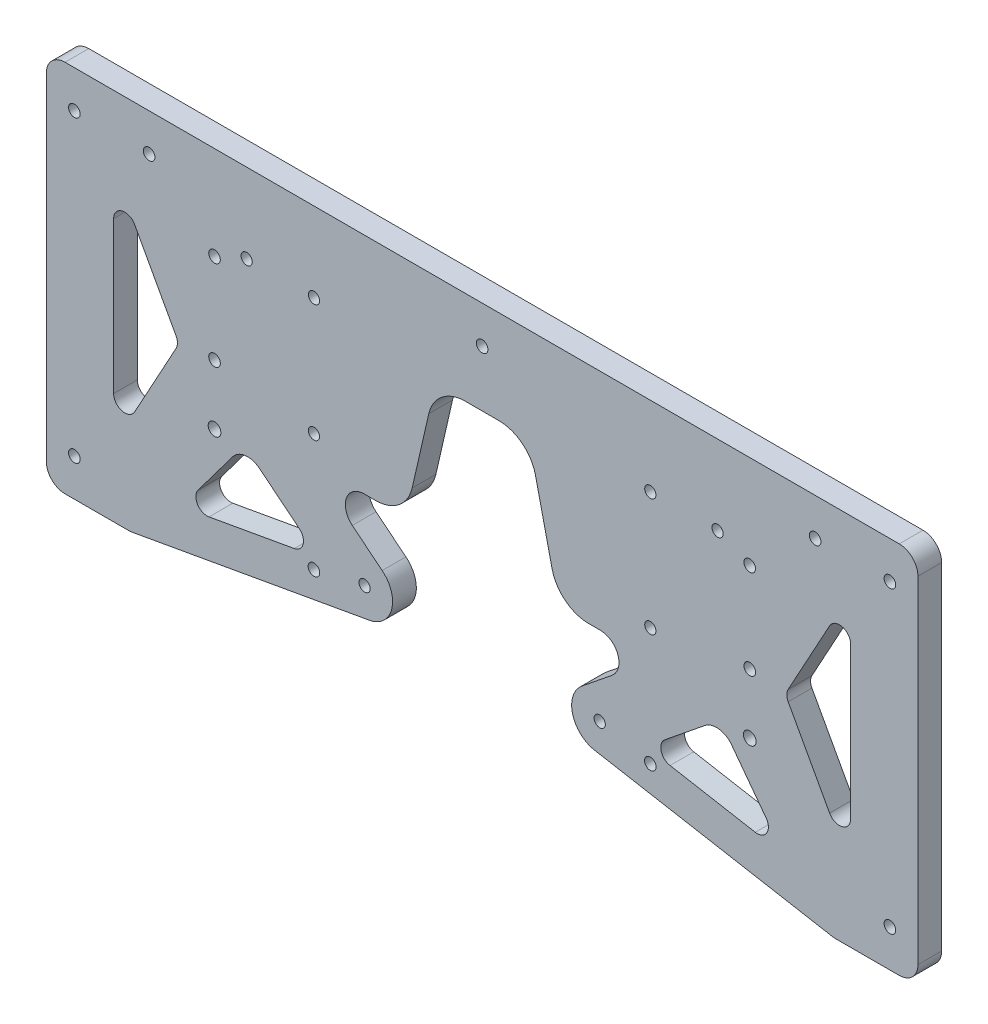
SolidWorks part; units mm, degrees
ref_plane "Front Plane" through (0, 0, 0) normal (0, 0, 1) x (1, 0, 0)
ref_plane "Top Plane" through (0, 0, 0) normal (0, 1, 0) x (1, 0, 0)
ref_plane "Right Plane" through (0, 0, 0) normal (1, 0, 0) x (0, 0, -1)
sketch "Sketch1" plane through (0, 0, 0) normal (0, 0, 1) x (1, 0, 0)
  line L0 (116.6, 0) -> (116.6, -35.2914) construction
  line L1 (0, 0) -> (233.2, 0)
  line L2 (0, 0) -> (0, -100)
  line L3 (0, -100) -> (233.2, -100)
  line L4 (233.2, 0) -> (233.2, -100)
  line L5 (0, 0) -> (15, 0)
  line L6 (0, 0) -> (0, -100)
  line L7 (0, -100) -> (15, -100)
  line L9 (233.2, 0) -> (218.2, 0)
  line L10 (233.2, 0) -> (233.2, -100)
  line L11 (233.2, -100) -> (218.2, -100)
  line L13 (0, -50) -> (37.696, -50) construction
  circle A0 centre (7.5, -10) radius 1.55
  circle A1 centre (225.7, -10) radius 1.55
  circle A2 centre (7.5, -90) radius 1.55
  circle A3 centre (225.7, -90) radius 1.55
  circle A4 centre (27.5, -10) radius 1.55
  circle A5 centre (205.7, -10) radius 1.55
  circle A6 centre (116.6, -10) radius 1.55
  dimension "D5" = 3.1
  dimension "D7" = 3.1
  dimension "D8" = 3.1
  dimension "D11" = 3.1
  dimension "D1" = 100
  dimension "D2" = 233.2
  dimension "D3" = 15
  dimension "D4" = 15
  dimension "D6" = 10
  dimension "D9" = 20
  dimension "D10" = 20
extrude "Boss-Extrude1" add sketch "Sketch1" along normal blind 6.35 contours L4 L1 L2 L3 A3 A1 A0 A2
fillet "Fillet1" radius 5 4 edges at (233.2, -100, 3.175) (0, -100, 3.175) (0, 0, 3.175) (233.2, 0, 3.175)
sketch "Sketch2" plane through (0, 0, 6.35) normal (0, 0, 1) x (1, 0, 0)
  line L0 (116.6, 0) -> (116.6, -100) construction
  line L1 (5, 0) -> (228.2, 0) construction
  line L2 (5, -100) -> (228.2, -100) construction
  line L3 (0, -5) -> (0, -95) construction
  circle A0 centre (45, -25) radius 1.55
  circle A1 centre (45, -49) radius 1.55
  circle A2 centre (188.2, -49) radius 1.55
  circle A3 centre (188.2, -25) radius 1.55
  dimension "D1" = 3.1
  dimension "D3" = 3.1
  dimension "D2" = 45
  dimension "D4" = 24
  dimension "D5" = 25
extrude "Cut-Extrude1" cut sketch "Sketch2" against normal blind 6.35 contours A0 | A1 | A2 | A3
sketch "Sketch3" plane through (0, 0, 6.35) normal (0, 0, 1) x (1, 0, 0)
  line L0 (5, 0) -> (228.2, 0) construction
  line L1 (120.7236, 0) -> (130.7236, 0)
  line L2 (120.7236, 0) -> (120.7236, 12.7)
  line L3 (120.7236, 12.7) -> (130.7236, 12.7)
  line L4 (130.7236, 0) -> (130.7236, 12.7)
  line L5 (130.7236, 24.7) -> (152.3136, 0)
  line L6 (130.7236, 12.7) -> (85.7236, 12.7)
  line L7 (130.7236, 12.7) -> (130.7236, 24.7)
  line L8 (130.7236, 24.7) -> (85.7236, 24.7)
  line L9 (85.7236, 12.7) -> (85.7236, 24.7)
  line L10 (120.7236, 12.7) -> (95.7236, 12.7)
  line L11 (120.7236, 12.7) -> (120.7236, 16.7)
  line L12 (120.7236, 16.7) -> (95.7236, 16.7)
  line L13 (95.7236, 12.7) -> (95.7236, 16.7)
  line M11 (228.2, 0) -> (5, 0)
  dimension "D1" = 12.7
  dimension "D2" = 10
  dimension "D3" = 12
  dimension "D4" = 45
  dimension "D5" = 25
  dimension "D6" = 4
extrude "Boss-Extrude2" add sketch "Sketch3" against normal up to surface (6.35 mm away) contours L4 L3 L2 M11 | L6 L13 L12 L11 L3 L7 L8 L9 | L7 L4 L5 M11 up to face at (46.55, -49, 0)
fillet "Fillet2" radius 5 1 edges at (85.7236, 12.7, 3.175)
fillet "Fillet3" radius 10 1 edges at (120.7236, 0, 3.175)
fillet "Fillet4" radius 2 1 edges at (85.7236, 24.7, 3.175)
fillet "Fillet5" radius 20 2 edges at (130.7236, 24.7, 3.175) (152.3136, 0, 3.175)
fillet "Fillet6" radius 5 1 edges at (120.7236, 16.7, 3.175)
sketch "Sketch4" plane through (0, 0, 0) normal (0, 0, -1) x (-1, 0, 0)
  line L12 (-110.7236, 0) -> (-161.3952, 0)
  line L24 (-136.7003, 17.8623) -> (-146.3368, 6.8377)
  line L25 (-87.7236, 24.7) -> (-121.642, 24.7)
  line L26 (-85.7236, 17.7) -> (-85.7236, 22.7)
  line L27 (-95.7236, 12.7) -> (-90.7236, 12.7)
  line L28 (-95.7236, 16.7) -> (-95.7236, 12.7)
  line L29 (-115.7236, 16.7) -> (-95.7236, 16.7)
  line L30 (-120.7236, 10) -> (-120.7236, 11.7)
  line L31 (-5, 0) -> (-110.7236, 0)
  line L32 (0, -95) -> (0, -5)
  line L33 (-228.2, -100) -> (-5, -100)
  line L34 (-233.2, -5) -> (-233.2, -95)
  line L35 (-161.3952, 0) -> (-228.2, 0)
  line L36 (-136.7003, 17.8623) -> (-146.3368, 6.8377)
  line L37 (-87.7236, 24.7) -> (-121.642, 24.7)
  line L38 (-85.7236, 17.7) -> (-85.7236, 22.7)
  line L39 (-95.7236, 12.7) -> (-90.7236, 12.7)
  line L40 (-95.7236, 16.7) -> (-95.7236, 12.7)
  line L41 (-115.7236, 16.7) -> (-95.7236, 16.7)
  line L42 (-120.7236, 10) -> (-120.7236, 11.7)
  line L43 (-5, 0) -> (-110.7236, 0)
  line L44 (0, -95) -> (0, -5)
  line L45 (-228.2, -100) -> (-5, -100)
  line L46 (-233.2, -5) -> (-233.2, -95)
  line L47 (-161.3952, 0) -> (-228.2, 0)
  arc A20 (-121.642, 24.7) -> (-136.7003, 17.8623) centre (-121.642, 4.7) ccw
  arc A21 (-85.7236, 22.7) -> (-87.7236, 24.7) centre (-87.7236, 22.7) ccw
  arc A22 (-90.7236, 12.7) -> (-85.7236, 17.7) centre (-90.7236, 17.7) ccw
  arc A23 (-115.7236, 16.7) -> (-120.7236, 11.7) centre (-115.7236, 11.7) ccw
  arc A24 (-120.7236, 10) -> (-110.7236, 0) centre (-110.7236, 10) ccw
  arc A25 (0, -5) -> (-5, 0) centre (-5, -5) ccw
  arc A26 (-5, -100) -> (0, -95) centre (-5, -95) ccw
  arc A27 (-233.2, -95) -> (-228.2, -100) centre (-228.2, -95) ccw
  arc A28 (-228.2, 0) -> (-233.2, -5) centre (-228.2, -5) ccw
  arc A29 (-161.3952, 0) -> (-146.3368, 6.8377) centre (-161.3952, 20) ccw
  arc A30 (-121.642, 24.7) -> (-136.7003, 17.8623) centre (-121.642, 4.7) ccw
  arc A31 (-85.7236, 22.7) -> (-87.7236, 24.7) centre (-87.7236, 22.7) ccw
  arc A32 (-90.7236, 12.7) -> (-85.7236, 17.7) centre (-90.7236, 17.7) ccw
  arc A33 (-115.7236, 16.7) -> (-120.7236, 11.7) centre (-115.7236, 11.7) ccw
  arc A34 (-120.7236, 10) -> (-110.7236, 0) centre (-110.7236, 10) ccw
  arc A35 (0, -5) -> (-5, 0) centre (-5, -5) ccw
  arc A36 (-5, -100) -> (0, -95) centre (-5, -95) ccw
  arc A37 (-233.2, -95) -> (-228.2, -100) centre (-228.2, -95) ccw
  arc A38 (-228.2, 0) -> (-233.2, -5) centre (-228.2, -5) ccw
  arc A39 (-161.3952, 0) -> (-146.3368, 6.8377) centre (-161.3952, 20) ccw
  line M31 (-87.7236, 24.7) -> (-121.642, 24.7)
  arc M32 (-121.642, 24.7) -> (-136.7003, 17.8623) centre (-121.642, 4.7) ccw
  line M33 (-136.7003, 17.8623) -> (-146.3368, 6.8377)
  arc M34 (-146.3368, 6.8377) -> (-161.3952, 0) centre (-161.3952, 20) cw
  arc M44 (-110.7236, 0) -> (-120.7236, 10) centre (-110.7236, 10) cw
  line M45 (-120.7236, 10) -> (-120.7236, 11.7)
  arc M46 (-120.7236, 11.7) -> (-115.7236, 16.7) centre (-115.7236, 11.7) cw
  line M47 (-115.7236, 16.7) -> (-95.7236, 16.7)
  line M48 (-95.7236, 16.7) -> (-95.7236, 12.7)
  line M49 (-95.7236, 12.7) -> (-90.7236, 12.7)
  arc M50 (-90.7236, 12.7) -> (-85.7236, 17.7) centre (-90.7236, 17.7) ccw
  line M51 (-85.7236, 17.7) -> (-85.7236, 22.7)
  arc M52 (-85.7236, 22.7) -> (-87.7236, 24.7) centre (-87.7236, 22.7) ccw
  dimension "D1" = 0
extrude "Cut-Extrude2" cut sketch "Sketch4" against normal blind 10 contours L12 M44 M45 M46 M47 M48 M49 M50 M51 M52 M31 M32 M33 M34
sketch "Sketch5" plane through (0, 0, 6.35) normal (0, 0, 1) x (1, 0, 0)
  line L0 (5, -100) -> (228.2, -100) construction
  line L1 (56.6, -60) -> (176.6, -60)
  line L2 (56.6, -60) -> (56.6, -100)
  line L3 (56.6, -100) -> (176.6, -100)
  line L4 (176.6, -60) -> (176.6, -100)
  line L5 (56.6, -60) -> (176.6, -100) construction
  line L6 (56.6, -100) -> (176.6, -60) construction
  line L7 (56.6, -60) -> (26.6, -100)
  line L8 (176.6, -60) -> (206.6, -100)
  point P0 (116.6, -80)
  line M18 (5, -100) -> (228.2, -100)
  dimension "D1" = 40
  dimension "D2" = 120
  dimension "D3" = 0
  dimension "D4" = 50
  dimension "D5" = 50
extrude "Cut-Extrude4" cut sketch "Sketch5" against normal blind 10 contours L2 L7 M18 | L4 L1 L2 M18 | L8 L4 M18
sketch "Sketch6" plane through (0, 0, 6.35) normal (0, 0, 1) x (1, 0, 0)
  line L0 (56.6, -60) -> (176.6, -60) construction
  line L7 (86.6, -37) -> (95.7201, -37)
  circle A0 centre (71.6, -21.25) radius 1.5
  circle A1 centre (161.6, -21.25) radius 1.5
  circle A2 centre (161.6, -52.75) radius 1.5
  circle A3 centre (71.6, -52.75) radius 1.5
  point P0 (116.6, -37)
  dimension "D3" = 3
  dimension "D1" = 31.5
  dimension "D2" = 60
  dimension "D4" = 23
  dimension "D5" = 45
  dimension "D6" = 45
extrude "Cut-Extrude5" cut sketch "Sketch6" against normal blind 10 contours A1 | A0 | A3 | A2
fillet "Fillet7" radius 10 4 edges at (206.6, -100, 3.175) (26.6, -100, 3.175) (56.6, -60, 3.175) (176.6, -60, 3.175)
sketch "Sketch7" plane through (0, 0, 6.35) normal (0, 0, 1) x (1, 0, 0)
  line L0 (61.6, -60) -> (171.6, -60) construction
  line L1 (104.1, -60) -> (129.1, -60)
  line L2 (104.1, -60) -> (104.1, -25)
  line L3 (104.1, -25) -> (129.1, -25)
  line L4 (129.1, -60) -> (129.1, -25)
  line L5 (104.1, -60) -> (129.1, -25) construction
  line L6 (104.1, -25) -> (129.1, -60) construction
  line L7 (104.1, -60) -> (96.1, -60)
  line L8 (129.1, -60) -> (137.1, -60)
  line L9 (137.1, -60) -> (129.1, -25)
  line L10 (104.1, -25) -> (96.1, -60)
  point P0 (116.6, -42.5)
  line M17 (61.6, -60) -> (171.6, -60)
  dimension "D1" = 35
  dimension "D2" = 25
  dimension "D3" = 17.5
  dimension "D4" = 8
  dimension "D5" = 8
extrude "Cut-Extrude6" cut sketch "Sketch7" against normal blind 10 contours L2 L10 M17 | L9 L4 M17 | L4 L3 L2 M17
fillet "Fillet9" radius 10 4 edges at (137.1, -60, 3.175) (96.1, -60, 3.175) (129.1, -25, 3.175) (104.1, -25, 3.175)
sketch "Sketch8" plane through (0, 0, 6.35) normal (0, 0, 1) x (1, 0, 0)
  line L0 (116.6, -10) -> (116.6, -54.0505) construction
  circle A0 centre (53.6, -21.25) radius 1.5
  circle A1 centre (71.6, -21.25) radius 1.5 construction
  circle A2 centre (179.6, -21.25) radius 1.5
  dimension "D1" = 3
  dimension "D2" = 18
extrude "Cut-Extrude7" cut sketch "Sketch8" against normal blind 10
sketch "Sketch9" plane through (0, 0, 6.35) normal (0, 0, 1) x (1, 0, 0)
  line L2 (83.9764, -80.2471) -> (85.1429, -81.1901)
  line L3 (85.1429, -81.1901) -> (83.9764, -80.2471)
  line L4 (52.8053, -64.6944) -> (80.4281, -87.0228)
  line L5 (70.8589, -60) -> (89.8577, -75.3574)
  line L6 (57.5201, -58.8617) -> (85.1429, -81.1901) construction
  line L7 (61.6, -60) -> (70.8589, -60)
  line L8 (61.6, -60) -> (88.1278, -60) construction
  line L9 (53.6, -64) -> (52.9758, -64.8322)
  line L10 (53.6, -64) -> (29.6, -96) construction
  line L11 (62.2349, -53.029) -> (89.8577, -75.3574) construction
  circle A0 centre (85.1429, -81.1901) radius 1.5
  circle A1 centre (71.6, -52.75) radius 1.5 construction
  circle A2 centre (146.6, -84.25) radius 1.5
  arc A3 (80.4281, -87.0228) -> (89.8577, -75.3574) centre (85.1429, -81.1901) ccw
  circle A4 centre (146.6, -84.25) radius 5
  arc A5 (61.6, -60) -> (53.6, -64) centre (61.6, -70) ccw construction
  arc A6 (61.6, -60) -> (53.6, -64) centre (61.6, -70) ccw
  line M19 (29.6, -96) -> (53.6, -64)
  arc M20 (53.6, -64) -> (61.6, -60) centre (61.6, -70) cw
  line M21 (61.6, -60) -> (88.1278, -60)
  dimension "D1" = 3
  dimension "D3" = 3
  dimension "D4" = 15
  dimension "D5" = 10
  dimension "D2" = 31.5
extrude "Boss-Extrude3" add sketch "Sketch9" against normal up to surface (6.35 mm away) contours L4 A3 L5 A0 M21 M20 M19 up to face at (55.1, -21.25, 0)
ref_plane "Plane1" through (116.6, 0, 0) normal (-1, 0, 0) x (0, 0, 1)
mirror "Mirror1" about plane through (116.6, 0, 0) normal (-1, 0, 0) of "Boss-Extrude3"
fillet "Fillet10" radius 5 4 edges at (180.2242, -64.8322, 3.175) (52.9758, -64.8322, 3.175) (162.3411, -60, 3.175) (70.8589, -60, 3.175)
sketch "Sketch10" plane through (0, 0, 6.35) normal (0, 0, 1) x (1, 0, 0)
  line L0 (23.3583, -99.8442) -> (86.4616, -88.5733)
  line L1 (36.0335, -87.422) -> (72.7983, -80.8554)
  line L2 (57.0081, -68.0916) -> (80.4281, -87.0228) construction
  line L3 (49.8649, -68.9801) -> (29.6, -96) construction
  line L4 (72.7983, -80.8554) -> (80.4281, -87.0228)
  line L5 (36.0335, -87.422) -> (29.6, -96)
  line L6 (8.4716, -92.3449) -> (107.0672, -74.7346) construction
  line L7 (10.2299, -102.1891) -> (108.8255, -84.5788) construction
  arc A0 (80.4281, -87.0228) -> (89.8577, -75.3574) centre (85.1429, -81.1901) ccw construction
  arc A1 (21.6, -100) -> (29.6, -96) centre (21.6, -90) ccw construction
  arc A2 (80.4281, -87.0228) -> (86.4616, -88.5733) centre (85.1429, -81.1901) ccw
  arc A3 (21.6, -100) -> (29.6, -96) centre (21.6, -90) ccw
  dimension "D1" = 10
extrude "Boss-Extrude4" add sketch "Sketch10" against normal up to surface (6.35 mm away) contours A3 L0 A2 L4 L1 L5 up to face at (116.6, -62.3357, 0)
fillet "Fillet11" radius 3 2 edges at (36.0335, -87.422, 3.175) (72.7983, -80.8554, 3.175)
mirror "Mirror3" about plane through (116.6, 0, 0) normal (-1, 0, 0) of "Boss-Extrude4"
fillet "Fillet12" radius 3 2 edges at (160.4017, -80.8554, 3.175) (197.1665, -87.422, 3.175)
sketch "Sketch11" plane through (0, 0, 6.35) normal (0, 0, 1) x (1, 0, 0)
  line L0 (5, 0) -> (228.2, 0) construction
  line L1 (233.2, -5) -> (233.2, -95) construction
  line L2 (211.6, -100) -> (228.2, -100) construction
  line L3 (209.8417, -99.8442) -> (146.7384, -88.5733) construction
  line L4 (151.345, -68.8885) -> (143.3423, -75.3574) construction
  line L5 (145.0722, -60) -> (148.2019, -60) construction
  line L6 (135.3236, -52.2282) -> (130.8764, -32.7718) construction
  line L7 (112.0722, -25) -> (121.1278, -25) construction
  line L8 (102.3236, -32.7718) -> (97.8764, -52.2282) construction
  line L9 (84.9981, -60) -> (88.1278, -60) construction
  line L10 (81.855, -68.8885) -> (89.8577, -75.3574) construction
  line L11 (23.3583, -99.8442) -> (86.4616, -88.5733) construction
  line L12 (5, -100) -> (21.6, -100) construction
  line L13 (0, -5) -> (0, -95) construction
  line L14 (5, 0) -> (228.2, 0)
  line L15 (233.2, -5) -> (233.2, -95)
  line L16 (211.6, -100) -> (228.2, -100)
  line L17 (209.8417, -99.8442) -> (146.7384, -88.5733)
  line L18 (151.345, -68.8885) -> (143.3423, -75.3574)
  line L19 (145.0722, -60) -> (148.2019, -60)
  line L20 (135.3236, -52.2282) -> (130.8764, -32.7718)
  line L21 (112.0722, -25) -> (121.1278, -25)
  line L22 (102.3236, -32.7718) -> (97.8764, -52.2282)
  line L23 (84.9981, -60) -> (88.1278, -60)
  line L24 (81.855, -68.8885) -> (89.8577, -75.3574)
  line L25 (23.3583, -99.8442) -> (86.4616, -88.5733)
  line L26 (5, -100) -> (21.6, -100)
  line L27 (0, -5) -> (0, -95)
  line L28 (84.7761, -28.7609) -> (81.6956, -42.2383)
  line L29 (81.6956, -42.2383) -> (81.6956, -42.2383)
  line L30 (63.9651, -74.3065) -> (63.9651, -74.3065)
  line L31 (20.8912, -82) -> (63.9651, -74.3065)
  line L32 (18, -82) -> (20.8912, -82)
  line L33 (18, -18) -> (18, -82)
  line L34 (18, -18) -> (215.2, -18)
  line L35 (215.2, -18) -> (215.2, -82)
  line L36 (212.3088, -82) -> (215.2, -82)
  line L37 (212.3088, -82) -> (169.2349, -74.3065)
  line L38 (169.2349, -74.3065) -> (169.2349, -74.3065)
  line L39 (151.5044, -42.2383) -> (151.5044, -42.2383)
  line L40 (151.5044, -42.2383) -> (148.4239, -28.7609)
  line L41 (112.0722, -7) -> (121.1278, -7)
  line L42 (18, -50) -> (35.5, -50) construction
  line L43 (18, -18) -> (35.5, -50)
  line L44 (35.5, -50) -> (18, -82)
  line L45 (116.6, -18) -> (116.6, -46.4735) construction
  line L46 (197.7, -50) -> (215.2, -82)
  line L47 (215.2, -18) -> (197.7, -50)
  arc A0 (233.2, -5) -> (228.2, 0) centre (228.2, -5) ccw construction
  arc A1 (228.2, -100) -> (233.2, -95) centre (228.2, -95) ccw construction
  arc A2 (209.8417, -99.8442) -> (211.6, -100) centre (211.6, -90) ccw construction
  arc A3 (21.6, -100) -> (23.3583, -99.8442) centre (21.6, -90) ccw construction
  arc A4 (143.3423, -75.3574) -> (146.7384, -88.5733) centre (148.0571, -81.1901) ccw construction
  arc A5 (151.345, -68.8885) -> (148.2019, -60) centre (148.2019, -65) ccw construction
  arc A6 (135.3236, -52.2282) -> (145.0722, -60) centre (145.0722, -50) ccw construction
  arc A7 (130.8764, -32.7718) -> (121.1278, -25) centre (121.1278, -35) ccw construction
  arc A8 (112.0722, -25) -> (102.3236, -32.7718) centre (112.0722, -35) ccw construction
  arc A9 (88.1278, -60) -> (97.8764, -52.2282) centre (88.1278, -50) ccw construction
  arc A10 (84.9981, -60) -> (81.855, -68.8885) centre (84.9981, -65) ccw construction
  arc A11 (86.4616, -88.5733) -> (89.8577, -75.3574) centre (85.1429, -81.1901) ccw construction
  arc A12 (0, -95) -> (5, -100) centre (5, -95) ccw construction
  arc A13 (5, 0) -> (0, -5) centre (5, -5) ccw construction
  arc A14 (233.2, -5) -> (228.2, 0) centre (228.2, -5) ccw
  arc A15 (228.2, -100) -> (233.2, -95) centre (228.2, -95) ccw
  arc A16 (209.8417, -99.8442) -> (211.6, -100) centre (211.6, -90) ccw
  arc A17 (21.6, -100) -> (23.3583, -99.8442) centre (21.6, -90) ccw
  arc A18 (143.3423, -75.3574) -> (146.7384, -88.5733) centre (148.0571, -81.1901) ccw
  arc A19 (151.345, -68.8885) -> (148.2019, -60) centre (148.2019, -65) ccw
  arc A20 (135.3236, -52.2282) -> (145.0722, -60) centre (145.0722, -50) ccw
  arc A21 (130.8764, -32.7718) -> (121.1278, -25) centre (121.1278, -35) ccw
  arc A22 (112.0722, -25) -> (102.3236, -32.7718) centre (112.0722, -35) ccw
  arc A23 (88.1278, -60) -> (97.8764, -52.2282) centre (88.1278, -50) ccw
  arc A24 (84.9981, -60) -> (81.855, -68.8885) centre (84.9981, -65) ccw
  arc A25 (86.4616, -88.5733) -> (89.8577, -75.3574) centre (85.1429, -81.1901) ccw
  arc A26 (0, -95) -> (5, -100) centre (5, -95) ccw
  arc A27 (5, 0) -> (0, -5) centre (5, -5) ccw
  arc A28 (81.6956, -42.2383) -> (81.6956, -42.2383) centre (81.6956, -42.2383) ccw
  arc A29 (81.6956, -42.2383) -> (63.9651, -74.3065) centre (84.9981, -65) ccw
  arc A30 (63.9651, -74.3065) -> (63.9651, -74.3065) centre (63.9651, -74.3065) ccw
  arc A31 (20.8912, -82) -> (20.8912, -82) centre (20.8912, -82) ccw
  arc A32 (18, -82) -> (18, -82) centre (18, -82) ccw
  arc A33 (18, -18) -> (18, -18) centre (18, -18) ccw
  arc A34 (215.2, -18) -> (215.2, -18) centre (215.2, -18) ccw
  arc A35 (215.2, -82) -> (215.2, -82) centre (215.2, -82) ccw
  arc A36 (212.3088, -82) -> (212.3088, -82) centre (212.3088, -82) ccw
  arc A37 (169.2349, -74.3065) -> (169.2349, -74.3065) centre (169.2349, -74.3065) ccw
  arc A38 (169.2349, -74.3065) -> (151.5044, -42.2383) centre (148.2019, -65) ccw
  arc A39 (151.5044, -42.2383) -> (151.5044, -42.2383) centre (151.5044, -42.2383) ccw
  arc A40 (148.4239, -28.7609) -> (121.1278, -7) centre (121.1278, -35) ccw
  arc A41 (112.0722, -7) -> (84.7761, -28.7609) centre (112.0722, -35) ccw
  dimension "D2" = 17.5
  dimension "D1" = 18
extrude "Cut-Extrude8" cut sketch "Sketch11" against normal blind 10 contours L44 L43 L33 | L35 L47 L46
fillet "Fillet13" radius 3 6 edges at (197.7, -50, 3.175) (215.2, -82, 3.175) (215.2, -18, 3.175) (18, -82, 3.175) (35.5, -50, 3.175) (18, -18, 3.175)
sketch "Sketch12" plane through (0, 0, 6.35) normal (0, 0, 1) x (1, 0, 0)
  arc A0 (186.5, -65) -> (189.9, -65) centre (188.2, -65) ccw construction
  arc A1 (189.9, -65) -> (186.5, -65) centre (188.2, -65) ccw construction
  arc A2 (43.3, -65) -> (46.7, -65) centre (45, -65) ccw construction
  arc A3 (46.7, -65) -> (43.3, -65) centre (45, -65) ccw construction
  arc A4 (186.5, -65) -> (189.9, -65) centre (188.2, -65) ccw
  arc A5 (189.9, -65) -> (186.5, -65) centre (188.2, -65) ccw
  arc A6 (43.3, -65) -> (46.7, -65) centre (45, -65) ccw
  arc A7 (46.7, -65) -> (43.3, -65) centre (45, -65) ccw
  circle A8 centre (85.1429, -81.1901) radius 1.5 construction
  circle A9 centre (148.0571, -81.1901) radius 1.5 construction
  circle A10 centre (85.1429, -81.1901) radius 1.5
  circle A11 centre (148.0571, -81.1901) radius 1.5
extrude "Cut-Extrude9" cut sketch "Sketch12" against normal blind 10 contours A4 A5 | A6 A7
sketch "Sketch13" plane through (0, 0, 6.35) normal (0, 0, 1) x (1, 0, 0)
  circle A0 centre (161.6, -84.25) radius 1.55 construction
  circle A1 centre (71.6, -84.25) radius 1.55 construction
  circle A2 centre (161.6, -84.25) radius 1.55
  circle A3 centre (71.6, -84.25) radius 1.55
extrude "Cut-Extrude10" cut sketch "Sketch13" against normal blind 10
